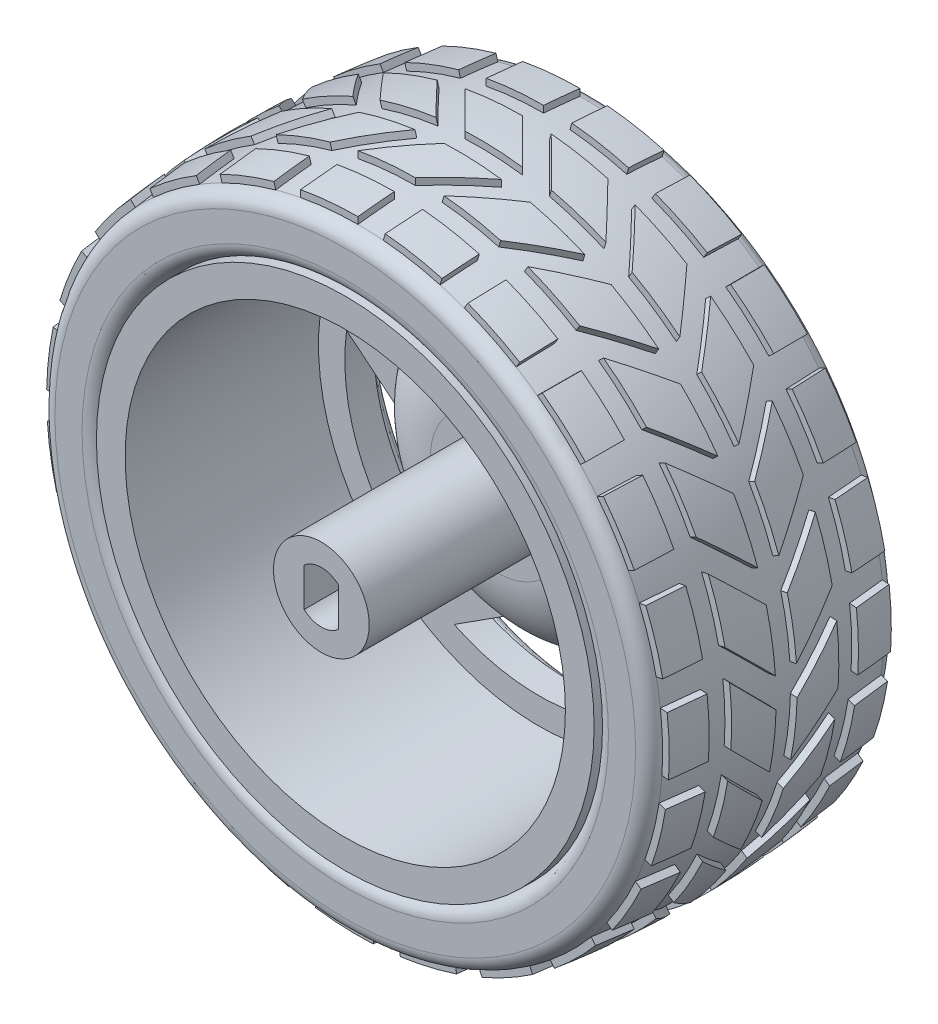
SolidWorks part; units mm, degrees
ref_plane "Front Plane" through (0, 0, 0) normal (0, 0, 1) x (1, 0, 0)
ref_plane "Top Plane" through (0, 0, 0) normal (0, 1, 0) x (1, 0, 0)
ref_plane "Right Plane" through (0, 0, 0) normal (1, 0, 0) x (0, 0, -1)
sketch "Sketch1" plane through (0, 0, 0) normal (1, 0, 0) x (0, 0, -1)
  line L0 (0, 0) -> (31.68, 0) construction
  line L1 (0, 0) -> (0, 5)
  line L2 (0, 5) -> (18.4, 5)
  line L3 (18.4, 5) -> (18.4, 7)
  line L4 (2.5, 26) -> (29, 26)
  line L5 (29, 26) -> (29, 24.5)
  line L6 (28.2, 22.5) -> (25.7, 22.5)
  line L7 (24.5, 0) -> (24.5, 5)
  line L8 (24.5, 5) -> (22.4, 5)
  line L9 (22.4, 5) -> (22.4, 7)
  line L10 (27.5, 12.1) -> (27.5, 19)
  line L11 (0, 0) -> (24.5, 0)
  line L12 (29, 24.5) -> (28.2, 24.5)
  line L13 (28.2, 24.5) -> (28.2, 22.5)
  line L14 (27.5, 12.1) -> (35.6714, 12.1) construction
  line L15 (2.5, 23) -> (22.7, 23)
  line L16 (22.7, 23) -> (22.7, 14.7311)
  line L17 (2.5, 23) -> (2.5, 26)
  arc A0 (22.4, 7) -> (27.5, 12.1) centre (27.5, 7) cw
  arc A1 (27.5, 19) -> (25.7, 22.5) centre (23.1972, 19) ccw
  arc A2 (18.4, 7) -> (22.7, 14.7311) centre (27.5, 7) cw
  dimension "D1" = 52
  dimension "D14" = 3
  dimension "D16" = 4
  dimension "D2" = 10
  dimension "D3" = 10
  dimension "D4" = 3
  dimension "D5" = 1.5
  dimension "D6" = 0.8
  dimension "D7" = 1.5
  dimension "D8" = 3.5
  dimension "D9" = 29
  dimension "D10" = 2
  dimension "D11" = 5.1
  dimension "D12" = 2.5
  dimension "D13" = 3.5
  dimension "D15" = 26.5
  dimension "D17" = 3
revolve "Revolve1" add sketch "Sketch1" angle 360 about L0
sketch "Sketch2" plane through (0, 0, -27.5) normal (0, 0, -1) x (-1, 0, 0)
  line L0 (0, 0) -> (0, 22.5) construction
  line L1 (0, 22.5) -> (-21.3988, 6.9529)
  line L2 (-21.3988, 6.9529) -> (-13.2252, -18.2029)
  line L3 (-13.2252, -18.2029) -> (13.2252, -18.2029)
  line L4 (13.2252, -18.2029) -> (21.3988, 6.9529)
  line L5 (21.3988, 6.9529) -> (0, 22.5)
  line L6 (0, 0) -> (-21.3988, 6.9529) construction
  line L7 (-20.4361, 9.4136) -> (-10.9391, 9.9525)
  line L8 (-2.6377, 22.3449) -> (-6.085, 13.4792)
  line L9 (0, 0) -> (-17.1718, 23.6349) construction
  line L12 (-10.9391, 9.9525) -> (-6.085, 13.4792) construction
  circle A0 centre (0, 0) radius 18.2029 construction
  circle A2 centre (0, 0) radius 22.5 construction
  circle A3 centre (0, 0) radius 22.5 construction
  arc A4 (-10.9391, 9.9525) -> (-6.085, 13.4792) centre (-11.2533, 15.4888) ccw
  circle A5 centre (0, 0) radius 12.1 construction
  circle A6 centre (0, 0) radius 22.5
  circle M6 centre (0, 0) radius 19
  dimension "D1" = 22
  dimension "D3" = 1.5
  dimension "D2" = 36
  dimension "D4" = 6
extrude "Cut-Extrude1" cut sketch "Sketch2" against normal up to next contours L8 A6 L7 L1 M6 | L7 A4 L8 L1 M6 | L1 M6 | L8 L1 M6 | L1 L7 M6
pattern_circular "CirPattern1" count 5 over 360 about axis through (0, 0, 0) along (0, 0, 1) of "Cut-Extrude1"
sketch "Sketch3" plane through (0, 0, -27.5) normal (0, 0, -1) x (-1, 0, 0)
  line L0 (0, 0) -> (0, 22.5) construction
  arc A0 (2.6377, 22.3449) -> (-2.6377, 22.3449) centre (0, 0) ccw construction
  circle A1 centre (0, 16.85) radius 0.75
  circle A2 centre (0, 0) radius 12.1 construction
  dimension "D1" = 4
  dimension "D2" = 1.5
extrude "Cut-Extrude2" cut sketch "Sketch3" against normal blind 1
pattern_circular "CirPattern2" count 5 over 360 about axis through (0, 0, 0) along (0, 0, 1) of "Cut-Extrude2"
sketch "Sketch4" plane through (0, 0, -22.4) normal (0, 0, -1) x (-1, 0, 0)
  line L0 (0, 0) -> (0, 10.5062) construction
  circle A0 centre (0, 0) radius 5 construction
  circle A1 centre (0, 0) radius 7 construction
  circle A2 centre (0, 0) radius 5 construction
  circle A3 centre (0, 0) radius 7 construction
  circle A4 centre (0, 0) radius 6 construction
  circle A5 centre (0, 6) radius 0.75
  dimension "D1" = 1
  dimension "D2" = 1.5
extrude "Boss-Extrude1" add sketch "Sketch4" along normal blind 1.5
pattern_circular "CirPattern3" count 4 over 360 about axis through (0, 0, 0) along (0, 0, 1) of "Boss-Extrude1"
fillet "Fillet1" radius 0.75 4 edges at (6, 0.75, -23.9) (0.75, -6, -23.9) (-6, -0.75, -23.9) (-0.75, 6, -23.9)
sketch "Sketch5" plane through (0, 0, 0) normal (0, 0, 1) x (1, 0, 0)
  line L0 (-1.8, 2.0125) -> (-1.8, -2.0125)
  line L2 (1.8, -2.0125) -> (1.8, 2.0125)
  circle A0 centre (0, 0) radius 2.7
  dimension "D1" = 5.4
  dimension "D2" = 3.6
extrude "Cut-Extrude3" cut sketch "Sketch5" against normal offset from surface (21.5 mm away) 3 contours L2 A0 L0 up to face at (5, 0, -24.5)
sketch "Sketch6" plane through (0, 0, -22.7) normal (0, 0, 1) x (1, 0, 0)
  circle A0 centre (0, 0) radius 20.25
  circle A1 centre (0, 0) radius 23 construction
  circle A2 centre (0, 0) radius 23
  dimension "D1" = 40.5
extrude "Boss-Extrude2" add sketch "Sketch6" against normal blind 3
fillet "Fillet2" radius 0.5 2 edges at (22.5, 0, -28.2) (24.5, 0, -29)
sketch "Sketch7" plane through (0, 0, 0) normal (1, 0, 0) x (0, 0, -1)
  line L0 (29, 26) -> (2.5, 26) construction
  line L1 (29, 26) -> (2.5, 26)
  line L2 (4, 26) -> (4, 19.2647) construction
  line L3 (27.5, 26) -> (27.5, 19.2647) construction
  line L4 (2.5, 26) -> (2.5, -26) construction
  line L5 (29, -26) -> (29, 26) construction
  line L6 (2.5, 26) -> (2.5, 42.0757) construction
  line L7 (28.35, 26) -> (28.35, 42.0757) construction
  line L8 (2.5, 30.3323) -> (2.5, 27.5)
  line L9 (28.35, 30.3323) -> (28.35, 27.5)
  line L10 (0, 0) -> (37.9684, 0) construction
  line L11 (0, 5) -> (0, -5) construction
  line L12 (15.425, 32.5) -> (47.3444, 32.5) construction
  line L13 (2.5, 30.3323) -> (28.35, 30.3323) construction
  line L14 (28.35, 27.5) -> (2.5, 27.5) construction
  arc A0 (4, 26) -> (2.5, 27.5) centre (4, 27.5) cw
  arc A1 (2.5, 31.6576) -> (28.35, 31.6576) centre (15.425, -67.0756) cw
  arc A2 (27.5, 26) -> (28.35, 27.5) centre (26.6015, 27.5) ccw
  arc A3 (3.8253, 31.8221) -> (2.5, 30.3323) centre (4, 30.3323) ccw
  arc A4 (27.0247, 31.8221) -> (28.35, 30.3323) centre (26.85, 30.3323) cw
  dimension "D4" = 32.5
  dimension "D1" = 1.5
  dimension "D2" = 1.5
  dimension "D3" = 0.65
revolve "Revolve2" add sketch "Sketch7" angle 360 about L10
ref_plane "Plane1" through (0, 35, 0) normal (0, 1, 0) x (1, 0, 0)
sketch "Sketch8" plane through (0, 35, 0) normal (0, 1, 0) x (1, 0, 0)
  line L0 (0, 0) -> (0, 38.366) construction
  line L1 (-5, 0) -> (5, 0) construction
  line L2 (26.5551, 27.0247) -> (26.5551, 3.8253) construction
  line L3 (31.8221, 27.0247) -> (-31.8221, 27.0247) construction
  line L4 (31.8221, 3.8253) -> (-31.8221, 3.8253) construction
  line L5 (26.5551, 15.425) -> (0, 15.425) construction
  line L6 (-6, 27.0247) -> (0, 27.0247)
  line L7 (0, 27.0247) -> (0, 23.225)
  line L8 (0, 23.225) -> (-6, 23.225)
  line L9 (-6, 23.225) -> (-6, 27.0247)
  line L10 (0, 3.8253) -> (0, 7.625)
  line L11 (0, 7.625) -> (-6, 7.625)
  line L12 (-6, 7.625) -> (-6, 3.8253)
  line L13 (-6, 3.8253) -> (0, 3.8253)
  line L14 (-6, 21.025) -> (0, 21.025)
  line L15 (0, 21.025) -> (4.5, 16.525)
  line L16 (4.5, 16.525) -> (-1.5, 16.525)
  line L17 (-1.5, 16.525) -> (-6, 21.025)
  line L18 (-1.5, 14.325) -> (4.5, 14.325)
  line L19 (4.5, 14.325) -> (0, 9.825)
  line L20 (0, 9.825) -> (-6, 9.825)
  line L21 (-6, 9.825) -> (-1.5, 14.325)
  line L22 (-6, 23.225) -> (-6, 21.025) construction
  line L23 (-6, 9.825) -> (-6, 7.625) construction
  line L24 (-6, 21.025) -> (-6, 9.825) construction
  line L25 (-1.5, 16.525) -> (-1.5, 14.325) construction
  line L26 (4.5, 16.525) -> (4.5, 14.325) construction
  dimension "D1" = 2.2
  dimension "D2" = 2.2
  dimension "D3" = 2.2
  dimension "D4" = 6
  dimension "D5" = 4.5
extrude "Boss-Extrude3" add sketch "Sketch8" against normal up to surface (3.37 mm away)
pattern_circular "CirPattern4" count 23 over 360 about axis through (0, 0, 0) along (0, 0, 1) of "Boss-Extrude3"
sketch "Sketch9" plane through (0, 0, 0) normal (1, 0, 0) x (0, 0, -1)
  line L0 (28.35, 30.3323) -> (28.35, 27.5) construction
  line L1 (2.5, 30.3323) -> (2.5, 27.5) construction
  line L2 (29, 26) -> (2.5, 26) construction
  line L3 (28.35, 30.3323) -> (28.35, 27.5) construction
  line L4 (2.5, 30.3323) -> (2.5, 27.5) construction
  line L5 (29, 26) -> (2.5, 26) construction
  line L6 (2.4091, 32.3517) -> (2.4091, 40.815)
  line L7 (2.4091, 40.815) -> (28.4409, 40.815)
  line L8 (28.4409, 40.815) -> (28.4409, 32.3517)
  line L9 (0, 0) -> (55.1944, 0) construction
  arc A1 (27.5, 26) -> (28.35, 27.5) centre (26.6015, 27.5) ccw construction
  arc A2 (28.35, 30.3323) -> (27.0247, 31.8221) centre (26.85, 30.3323) ccw construction
  arc A3 (28.35, 31.6576) -> (2.5, 31.6576) centre (15.425, -67.0756) ccw construction
  arc A4 (2.5, 27.5) -> (4, 26) centre (4, 27.5) ccw construction
  arc A5 (3.8253, 31.8221) -> (2.5, 30.3323) centre (4, 30.3323) ccw construction
  arc A6 (27.5, 26) -> (28.35, 27.5) centre (26.6015, 27.5) ccw construction
  arc A7 (28.35, 30.3323) -> (27.0247, 31.8221) centre (26.85, 30.3323) ccw construction
  arc A8 (28.35, 31.6576) -> (2.5, 31.6576) centre (15.425, -67.0756) ccw construction
  arc A9 (2.5, 27.5) -> (4, 26) centre (4, 27.5) ccw construction
  arc A10 (3.8253, 31.8221) -> (2.5, 30.3323) centre (4, 30.3323) ccw construction
  arc A11 (28.4409, 32.3517) -> (2.4091, 32.3517) centre (15.425, -67.0756) ccw
  dimension "D1" = 0.7
revolve "Cut-Revolve1" cut sketch "Sketch9" angle 360 about L9
